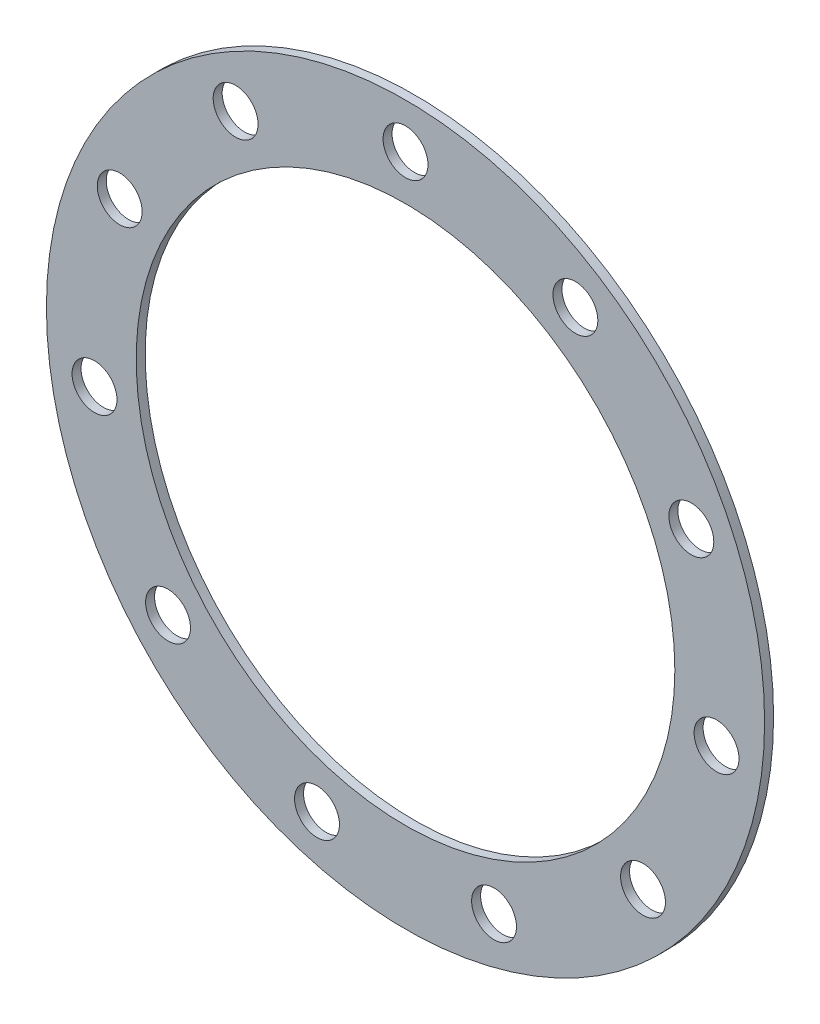
SolidWorks part; units mm, degrees
material "Acrylic (Medium-high impact)"
ref_plane "Front Plane" through (0, 0, 0) normal (0, 0, 1) x (1, 0, 0)
ref_plane "Top Plane" through (0, 0, 0) normal (0, 1, 0) x (1, 0, 0)
ref_plane "Right Plane" through (0, 0, 0) normal (1, 0, 0) x (0, 0, -1)
sketch "Sketch1" plane through (0, 0, 0) normal (0, 0, 1) x (1, 0, 0)
  circle A0 centre (0, 0) radius 40
  circle A1 centre (0, 0) radius 30
  circle A2 centre (0, 0) radius 35 construction
  circle A3 centre (0, 35) radius 2.5
  circle A4 centre (18.9224, 29.4439) radius 2.5
  circle A5 centre (31.8371, 14.5395) radius 2.5
  circle A6 centre (34.6438, -4.981) radius 2.5
  circle A7 centre (26.4512, -22.9201) radius 2.5
  circle A8 centre (9.8606, -33.5823) radius 2.5
  circle A9 centre (-9.8606, -33.5823) radius 2.5
  circle A10 centre (-26.4512, -22.9201) radius 2.5
  circle A11 centre (-34.6438, -4.981) radius 2.5
  circle A12 centre (-31.8371, 14.5395) radius 2.5
  circle A13 centre (-18.9224, 29.4439) radius 2.5
  point P29 (0, 0)
  dimension "D1" = 80
  dimension "D2" = 60
  dimension "D3" = 70
  dimension "D4" = 5
extrude "Boss-Extrude1" add sketch "Sketch1" along normal blind 1
